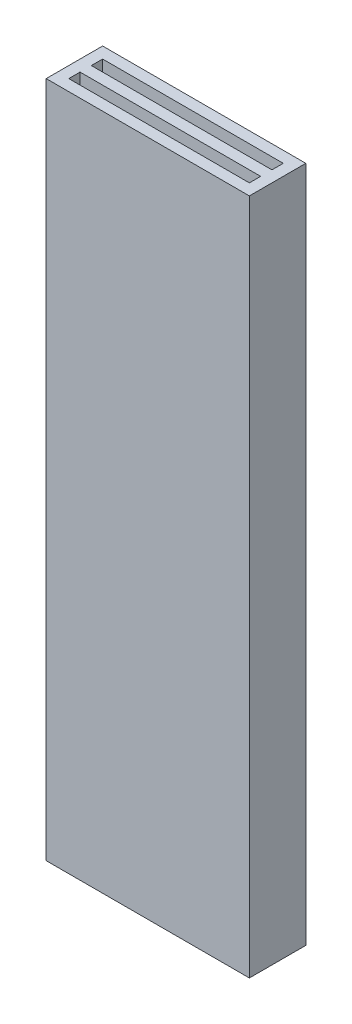
SolidWorks part; units mm, degrees
ref_plane "Front Plane" through (0, 0, 0) normal (0, 0, 1) x (1, 0, 0)
ref_plane "Top Plane" through (0, 0, 0) normal (0, 1, 0) x (1, 0, 0)
ref_plane "Right Plane" through (0, 0, 0) normal (1, 0, 0) x (0, 0, -1)
sketch "Sketch1" plane through (0, 0, 0) normal (0, 1, 0) x (1, 0, 0)
  line L1 (-4.5, -1.25) -> (4.5, -1.25)
  line L2 (-4.5, -1.25) -> (-4.5, 1.25)
  line L3 (-4.5, 1.25) -> (4.5, 1.25)
  line L4 (4.5, -1.25) -> (4.5, 1.25)
  line L5 (-4.5, -1.25) -> (4.5, 1.25) construction
  line L6 (-4.5, 1.25) -> (4.5, -1.25) construction
  point P0 (0, 0)
  dimension "D1" = 9
  dimension "D2" = 2.5
extrude "Boss-Extrude1" add sketch "Sketch1" along normal mid plane 30
sketch "Sketch2" plane through (0, 15, 0) normal (0, 1, 0) x (1, 0, 0)
  line L1 (-4, 0.25) -> (4, 0.25)
  line L2 (-4, 0.25) -> (-4, 0.75)
  line L3 (-4, 0.75) -> (4, 0.75)
  line L4 (4, 0.25) -> (4, 0.75)
  line L5 (-4, 0.25) -> (4, 0.75) construction
  line L6 (-4, 0.75) -> (4, 0.25) construction
  point P0 (0, 0.5)
  dimension "D1" = 0.5
  dimension "D2" = 8
  dimension "D3" = 0
  dimension "D4" = 0.5
extrude "Cut-Extrude1" cut sketch "Sketch2" against normal through all and the other way through all
mirror "Mirror1" about plane through (0, 0, 0) normal (0, 0, 1) of "Cut-Extrude1"
